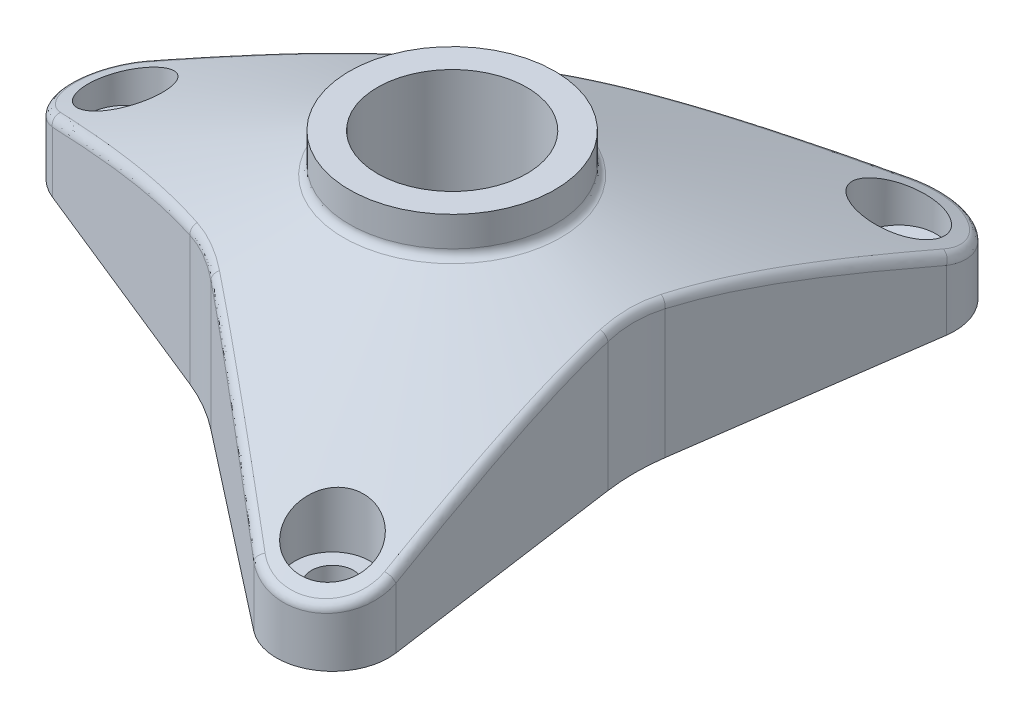
SolidWorks part; units mm, degrees
material "Plain Carbon Steel"
ref_plane "Front Plane" through (0, 0, 0) normal (0, 0, 1) x (1, 0, 0)
ref_plane "Top Plane" through (0, 0, 0) normal (0, 1, 0) x (1, 0, 0)
ref_plane "Right Plane" through (0, 0, 0) normal (1, 0, 0) x (0, 0, -1)
sketch "Sketch1" plane through (0, 0, 0) normal (0, 1, 0) x (1, 0, 0)
  line L0 (0, 0) -> (-35, 0) construction
  line L1 (0, 0) -> (17.5, 30.3109) construction
  line L2 (0, 0) -> (17.5, -30.3109) construction
  line L3 (-37.2476, 5.5631) -> (-9.6495, 16.7135)
  line L4 (-37.2476, -5.5631) -> (-9.6495, -16.7135)
  line L5 (23.4416, 29.4759) -> (19.299, 0)
  line L6 (13.806, 35.039) -> (-9.6495, 16.7135)
  line L7 (13.806, -35.039) -> (-9.6495, -16.7135)
  line L8 (23.4416, -29.4759) -> (19.299, 0)
  circle A0 centre (0, 0) radius 35 construction
  arc A1 (-37.2476, 5.5631) -> (-37.2476, -5.5631) centre (-35, 0) ccw
  arc A2 (23.4416, 29.4759) -> (13.806, 35.039) centre (17.5, 30.3109) ccw
  arc A3 (13.806, -35.039) -> (23.4416, -29.4759) centre (17.5, -30.3109) ccw
  point P22 (0, 0)
  dimension "D3" = 70
  dimension "D4" = 12
  dimension "D1" = 120
  dimension "D2" = 120
  dimension "D5" = 22
  dimension "D6" = 22
extrude "Boss-Extrude1" add sketch "Sketch1" along normal blind 22
sketch "Sketch2" plane through (0, 0, 0) normal (0, 0, 1) x (1, 0, 0)
  line L0 (0, 0) -> (0, 43.1739) construction
  line L1 (0, 22) -> (-11, 22)
  line L2 (-9.6495, 22) -> (13.806, 22) construction
  line L3 (-11, 22) -> (-11, 18.1208)
  line L4 (-11, 18.1208) -> (-41, 6)
  line L5 (-41, 22) -> (-41, 0) construction
  line L6 (-41, 6) -> (-41, 33.0737)
  line L7 (-41, 33.0737) -> (0, 33.0737)
  line L8 (0, 33.0737) -> (0, 22)
  dimension "D1" = 11
  dimension "D2" = 112
  dimension "D3" = 6
revolve "Cut-Revolve1" cut sketch "Sketch2" angle 360 about L0
sketch "Sketch3" plane through (0, 22, 0) normal (0, 1, 0) x (1, 0, 0)
  circle A0 centre (0, 0) radius 8
  dimension "D1" = 16
extrude "Cut-Extrude1" cut sketch "Sketch3" against normal through all
fillet "Fillet1" radius 22 3 edges at (19.299, 7.3839, 0) (-9.6495, 7.3839, -16.7135) (-9.6495, 7.3839, 16.7135)
sketch "Sketch4" plane through (0, 0, 0) normal (0, -1, 0) x (1, 0, 0)
  circle A0 centre (-35, 0) radius 2.25
  dimension "D1" = 4.5
extrude "Cut-Extrude2" cut sketch "Sketch4" against normal blind 4
pattern_circular "CirPattern1" count 3 over 360 about axis through (0, 0, 0) along (0, 1, 0) of "Cut-Extrude2"
sketch "Sketch5" plane through (0, 4, 0) normal (0, -1, 0) x (1, 0, 0)
  circle A0 centre (-35, 0) radius 4
  dimension "D1" = 8
extrude "Cut-Extrude3" cut sketch "Sketch5" against normal blind 16
pattern_circular "CirPattern2" count 3 over 360 about axis through (0, 0, 0) along (0, 1, 0) of "Cut-Extrude3"
fillet "Fillet2" radius 1 13 edges at (19.6235, 14.5879, -2.1793) (21.3151, 6.0283, 34.9418) (-7.9244, 14.5879, 18.084) (-40.918, 6.0283, 0.9885) (-11.699, 14.5879, -15.9048) (19.6029, 6.0283, -35.9303) (0, 18.1208, -11)
